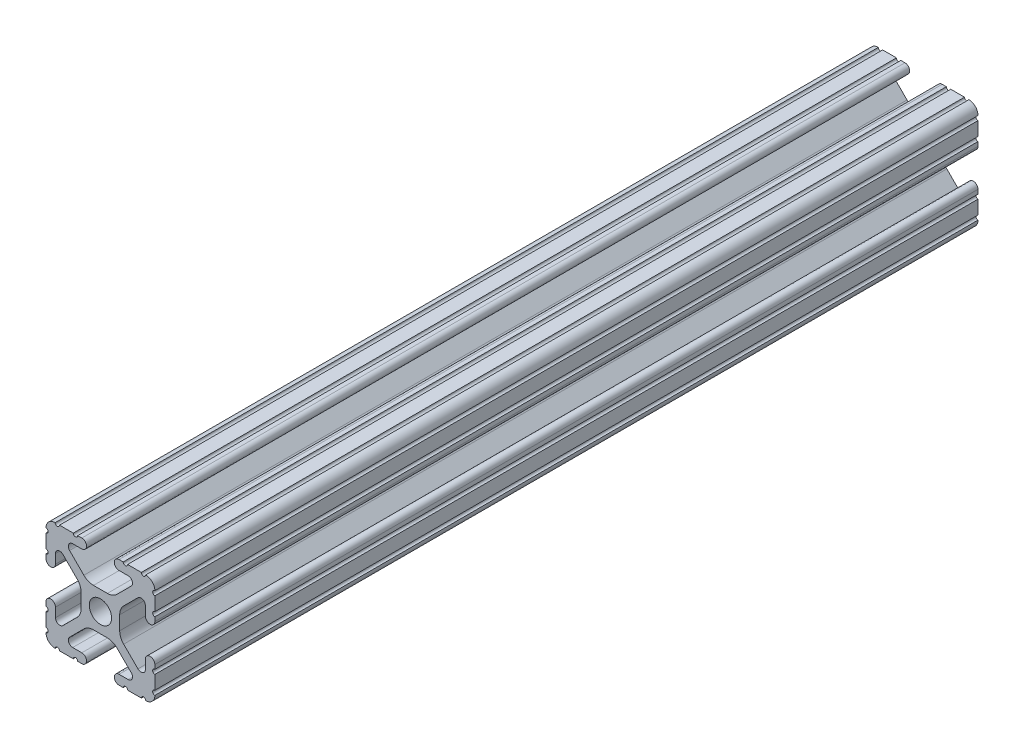
SolidWorks part; units mm, degrees
material "6061-T6 (SS)"
ref_plane "Front Plane" through (0, 0, 0) normal (0, 0, 1) x (1, 0, 0)
ref_plane "Top Plane" through (0, 0, 0) normal (0, 1, 0) x (1, 0, 0)
ref_plane "Right Plane" through (0, 0, 0) normal (1, 0, 0) x (0, 0, -1)
ref_plane "Plane1" through (0, 0, -450.85) normal (0, 0, -1) x (-1, 0, 0)
sketch "Sketch1" plane through (0, 0, -450.85) normal (0, 0, -1) x (-1, 0, 0)
  line L0 (12.7, -9.5504) -> (12.7, -6.3331)
  line L1 (12.7, -5.3171) -> (12.7, -4.3434)
  line L2 (10.4902, -4.3434) -> (10.4902, -6.4748)
  line L3 (8.7558, -7.1932) -> (5.4257, -3.8632)
  line L4 (4.4958, -1.6181) -> (4.4958, 1.6181)
  line L5 (5.4257, 3.8632) -> (8.7558, 7.1932)
  line L6 (10.4902, 6.4748) -> (10.4902, 4.3434)
  line L7 (12.7, 4.3434) -> (12.7, 5.3171)
  line L8 (12.7, 6.3331) -> (12.7, 9.5504)
  line L9 (9.5504, 12.7) -> (6.3331, 12.7)
  line L10 (5.3171, 12.7) -> (4.3434, 12.7)
  line L11 (4.3434, 10.4902) -> (6.4748, 10.4902)
  line L12 (7.1932, 8.7558) -> (3.8632, 5.4257)
  line L13 (1.6181, 4.4958) -> (-1.6181, 4.4958)
  line L14 (-3.8632, 5.4257) -> (-7.1932, 8.7558)
  line L15 (-6.4748, 10.4902) -> (-4.3434, 10.4902)
  line L16 (-4.3434, 12.7) -> (-5.3171, 12.7)
  line L17 (-6.3331, 12.7) -> (-9.5504, 12.7)
  line L18 (-12.7, 9.5504) -> (-12.7, 6.3331)
  line L19 (-12.7, 5.3171) -> (-12.7, 4.3434)
  line L20 (-10.4902, 4.3434) -> (-10.4902, 6.4748)
  line L21 (-8.7558, 7.1932) -> (-5.4257, 3.8632)
  line L22 (-4.4958, 1.6181) -> (-4.4958, -1.6181)
  line L23 (-5.4257, -3.8632) -> (-8.7558, -7.1932)
  line L24 (-10.4902, -6.4748) -> (-10.4902, -4.3434)
  line L25 (-12.7, -4.3434) -> (-12.7, -5.3171)
  line L26 (-12.7, -6.3331) -> (-12.7, -9.5504)
  line L27 (-9.5504, -12.7) -> (-6.3331, -12.7)
  line L28 (-5.3171, -12.7) -> (-4.3434, -12.7)
  line L29 (-4.3434, -10.4902) -> (-6.4748, -10.4902)
  line L30 (-7.1932, -8.7558) -> (-3.8632, -5.4257)
  line L31 (-1.6181, -4.4958) -> (1.6181, -4.4958)
  line L32 (3.8632, -5.4257) -> (7.1932, -8.7558)
  line L33 (6.4748, -10.4902) -> (4.3434, -10.4902)
  line L34 (4.3434, -12.7) -> (5.3171, -12.7)
  line L35 (6.3331, -12.7) -> (9.5504, -12.7)
  arc A0 (12.6998, -10.5664) -> (12.7, -9.5504) centre (12.7, -10.0584) cw
  arc A1 (12.7, -6.3331) -> (12.7, -5.3171) centre (12.7, -5.8251) cw
  arc A2 (12.7, -4.3434) -> (10.4902, -4.3434) centre (11.5951, -4.3434) ccw
  arc A3 (10.4902, -6.4748) -> (8.7558, -7.1932) centre (9.4742, -6.4748) cw
  arc A4 (5.4257, -3.8632) -> (4.4958, -1.6181) centre (7.6708, -1.6181) cw
  arc A5 (4.4958, 1.6181) -> (5.4257, 3.8632) centre (7.6708, 1.6181) cw
  arc A6 (8.7558, 7.1932) -> (10.4902, 6.4748) centre (9.4742, 6.4748) cw
  arc A7 (10.4902, 4.3434) -> (12.7, 4.3434) centre (11.5951, 4.3434) ccw
  arc A8 (12.7, 5.3171) -> (12.7, 6.3331) centre (12.7, 5.8251) cw
  arc A9 (12.7, 9.5504) -> (12.6998, 10.5664) centre (12.7, 10.0584) cw
  arc A10 (12.6998, 10.5664) -> (10.5664, 12.6998) centre (10.5918, 10.5918) ccw
  arc A11 (10.5664, 12.6998) -> (9.5504, 12.7) centre (10.0584, 12.7) cw
  arc A12 (6.3331, 12.7) -> (5.3171, 12.7) centre (5.8251, 12.7) cw
  arc A13 (4.3434, 12.7) -> (4.3434, 10.4902) centre (4.3434, 11.5951) ccw
  arc A14 (6.4748, 10.4902) -> (7.1932, 8.7558) centre (6.4748, 9.4742) cw
  arc A15 (3.8632, 5.4257) -> (1.6181, 4.4958) centre (1.6181, 7.6708) cw
  arc A16 (-1.6181, 4.4958) -> (-3.8632, 5.4257) centre (-1.6181, 7.6708) cw
  arc A17 (-7.1932, 8.7558) -> (-6.4748, 10.4902) centre (-6.4748, 9.4742) cw
  arc A18 (-4.3434, 10.4902) -> (-4.3434, 12.7) centre (-4.3434, 11.5951) ccw
  arc A19 (-5.3171, 12.7) -> (-6.3331, 12.7) centre (-5.8251, 12.7) cw
  arc A20 (-9.5504, 12.7) -> (-10.5664, 12.6998) centre (-10.0584, 12.7) cw
  arc A21 (-10.5664, 12.6998) -> (-12.6998, 10.5664) centre (-10.5918, 10.5918) ccw
  arc A22 (-12.6998, 10.5664) -> (-12.7, 9.5504) centre (-12.7, 10.0584) cw
  arc A23 (-12.7, 6.3331) -> (-12.7, 5.3171) centre (-12.7, 5.8251) cw
  arc A24 (-12.7, 4.3434) -> (-10.4902, 4.3434) centre (-11.5951, 4.3434) ccw
  arc A25 (-10.4902, 6.4748) -> (-8.7558, 7.1932) centre (-9.4742, 6.4748) cw
  arc A26 (-5.4257, 3.8632) -> (-4.4958, 1.6181) centre (-7.6708, 1.6181) cw
  arc A27 (-4.4958, -1.6181) -> (-5.4257, -3.8632) centre (-7.6708, -1.6181) cw
  arc A28 (-8.7558, -7.1932) -> (-10.4902, -6.4748) centre (-9.4742, -6.4748) cw
  arc A29 (-10.4902, -4.3434) -> (-12.7, -4.3434) centre (-11.5951, -4.3434) ccw
  arc A30 (-12.7, -5.3171) -> (-12.7, -6.3331) centre (-12.7, -5.8251) cw
  arc A31 (-12.7, -9.5504) -> (-12.6998, -10.5664) centre (-12.7, -10.0584) cw
  arc A32 (-12.6998, -10.5664) -> (-10.5664, -12.6998) centre (-10.5918, -10.5918) ccw
  arc A33 (-10.5664, -12.6998) -> (-9.5504, -12.7) centre (-10.0584, -12.7) cw
  arc A34 (-6.3331, -12.7) -> (-5.3171, -12.7) centre (-5.8251, -12.7) cw
  arc A35 (-4.3434, -12.7) -> (-4.3434, -10.4902) centre (-4.3434, -11.5951) ccw
  arc A36 (-6.4748, -10.4902) -> (-7.1932, -8.7558) centre (-6.4748, -9.4742) cw
  arc A37 (-3.8632, -5.4257) -> (-1.6181, -4.4958) centre (-1.6181, -7.6708) cw
  arc A38 (1.6181, -4.4958) -> (3.8632, -5.4257) centre (1.6181, -7.6708) cw
  arc A39 (7.1932, -8.7558) -> (6.4748, -10.4902) centre (6.4748, -9.4742) cw
  arc A40 (4.3434, -10.4902) -> (4.3434, -12.7) centre (4.3434, -11.5951) ccw
  arc A41 (5.3171, -12.7) -> (6.3331, -12.7) centre (5.8251, -12.7) cw
  arc A42 (9.5504, -12.7) -> (10.5664, -12.6998) centre (10.0584, -12.7) cw
  arc A43 (10.5664, -12.6998) -> (12.6998, -10.5664) centre (10.5918, -10.5918) ccw
  circle A44 centre (0, 0) radius 2.6035
extrude "Boss-Extrude1" add sketch "Sketch1" against normal mid plane 192.0875
